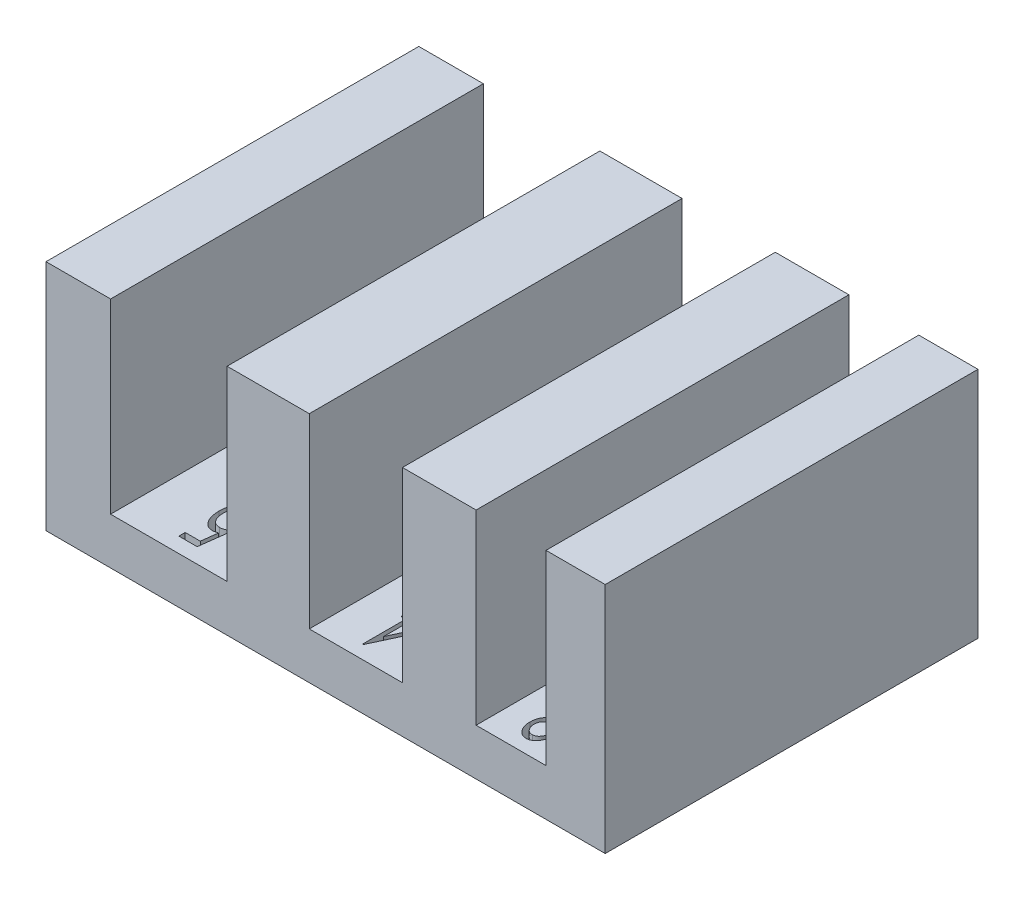
SolidWorks part; units mm, degrees
ref_plane "Front Plane" through (0, 0, 0) normal (0, 0, 1) x (1, 0, 0)
ref_plane "Top Plane" through (0, 0, 0) normal (0, 1, 0) x (1, 0, 0)
ref_plane "Right Plane" through (0, 0, 0) normal (1, 0, 0) x (0, 0, -1)
sketch "Sketch1" plane through (0, 0, 0) normal (0, 1, 0) x (1, 0, 0)
  line L0 (0, 0) -> (19.05, 0)
  line L2 (0, 0) -> (0, 12.7)
  line L3 (0, 12.7) -> (17.0337, 12.7)
  line L4 (19.05, 0) -> (19.05, 12.7)
  line L5 (2.2002, 12.7) -> (6.169, 12.7)
  line L6 (2.2002, 12.7) -> (2.2002, 0)
  line L7 (2.2002, 0) -> (6.169, 0)
  line L8 (6.169, 12.7) -> (6.169, 0)
  line L9 (8.9687, 12.7) -> (12.1437, 12.7)
  line L10 (8.9687, 12.7) -> (8.9687, 0)
  line L11 (8.9687, 0) -> (12.1437, 0)
  line L12 (12.1437, 12.7) -> (12.1437, 0)
  line L13 (14.6524, 12.7) -> (17.0337, 12.7)
  line L14 (14.6524, 12.7) -> (14.6524, 0)
  line L15 (14.6524, 0) -> (17.0337, 0)
  line L16 (17.0337, 12.7) -> (17.0337, 0)
  line L21 (17.0337, 12.7) -> (19.05, 12.7)
  dimension "D1" = 3.9688
  dimension "D2" = 3.175
  dimension "D3" = 2.3813
  dimension "D4" = 19.05
  dimension "D5" = 12.7
extrude "Boss-Extrude1" add sketch "Sketch1" along normal blind 6.35 contours L6 L3 L2 L0 | L10 L3 L8 L0 | L14 L3 L12 L0 | L21 L16 L0 L4
sketch "Sketch3" plane through (0, 0, 0) normal (0, 1, 0) x (1, 0, 0)
  line L1 (0, 12.7) -> (19.05, 12.7)
  line L2 (0, 12.7) -> (0, 0)
  line L3 (0, 0) -> (19.05, 0)
  line L4 (19.05, 12.7) -> (19.05, 0)
extrude "Boss-Extrude2" add sketch "Sketch3" against normal blind 1.5875
sketch "Sketch5" plane through (0, 0, 0) normal (0, -1, 0) x (1, 0, 0)
  line L3 (16.422, -12.7) -> (16.422, 0) construction
  line L4 (11.1934, -12.7) -> (11.1934, 0) construction
  line L5 (4.9861, -12.7) -> (4.9861, 0) construction
  text T0 "<r90>5/32</r>" font "Century Gothic" height in points 8
  text T1 "<r90>4/32</r>" font "Century Gothic" height in points 8
  text T2 "<r90>3/32</r>" font "Century Gothic" height in points 8
extrude "Cut-Extrude1" cut sketch "Sketch5" along normal blind 0.7937
